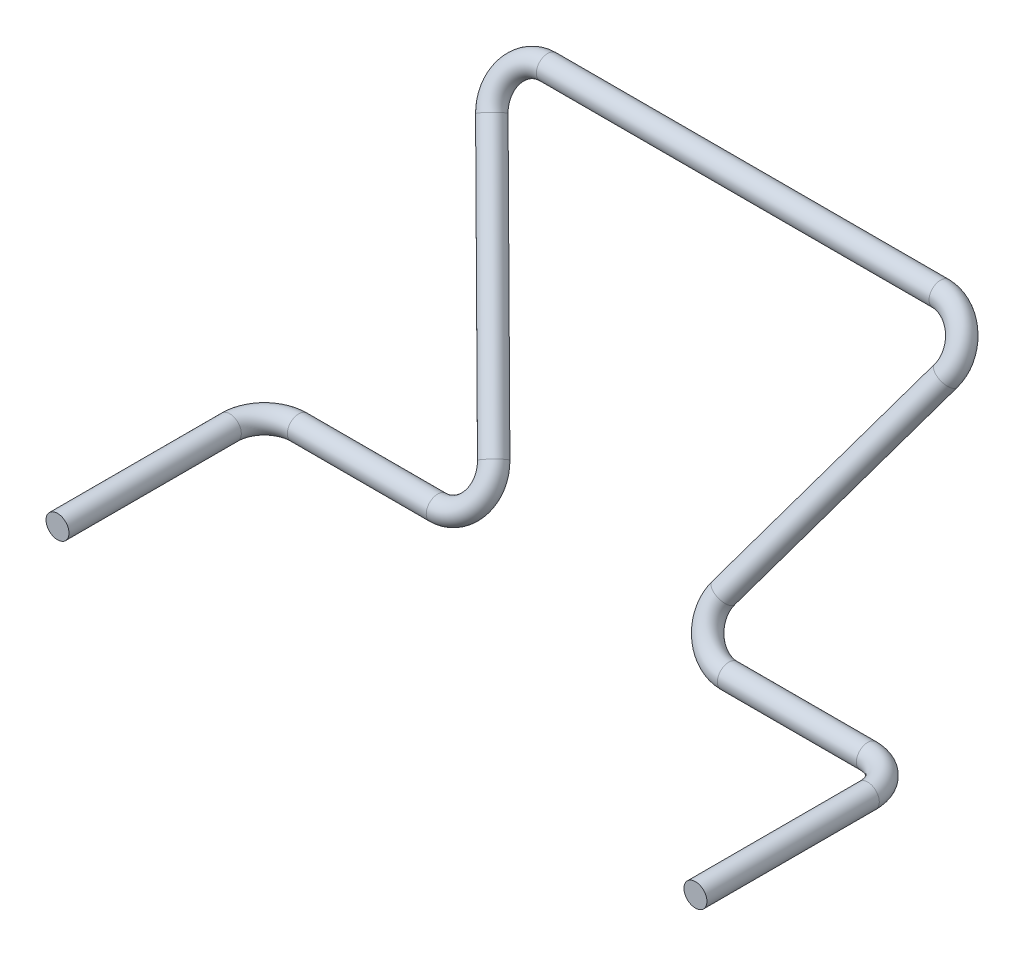
SolidWorks part; units mm, degrees
ref_plane "Front Plane" through (0, 0, 0) normal (0, 0, 1) x (1, 0, 0)
ref_plane "Top Plane" through (0, 0, 0) normal (0, 1, 0) x (1, 0, 0)
ref_plane "Right Plane" through (0, 0, 0) normal (1, 0, 0) x (0, 0, -1)
sketch3d "3DSketch2"
  line L0 (-27.7615, 0, 18) -> (-27.7615, 0, 3)
  line L1 (-24.7615, 0, 0) -> (-12.6698, 0, 0)
  line L2 (-10, 3.7731, -2.201) -> (-19.7615, 20.2269, -11.799)
  line L3 (-17.0917, 24, -14) -> (0, 24, -14)
  arc A0 (-19.7615, 20.2269, -11.799) -> (-17.0917, 24, -14) centre (-17.0917, 21.4087, -12.4884) ccw
  arc A1 (-12.6698, 0, 0) -> (-10, 3.7731, -2.201) centre (-12.6698, 2.5913, -1.5116) ccw
  arc A2 (-27.7615, 0, 3) -> (-24.7615, 0, 0) centre (-24.7615, 0, 3) ccw
  point P7 (-22, 24, -14)
  point P8 (-17.0917, 19.8971, -15.0797)
  point P11 (-7.7615, 0, 0)
  point P12 (-12.6698, 4.1029, 1.0797)
  point P15 (-27.7615, 0, 0)
  point P16 (-24.7615, -3, 3)
  point P17 (-5.8504, 0, 2.8877)
  point P18 (0, 0, 0)
  point P19 (0, 0, 0)
  point P20 (0.1262, 24, -14)
  point P21 (0, 0, 0)
  point P22 (-28.0539, 0, 22.7416)
  point P23 (-7.775, 0, 0.2142)
  point P24 (-24.7963, 0, 0.5516)
  point P25 (0, 0, 0)
  point P26 (0, 0, 0)
  point P27 (0, 0, 0)
  dimension "D1" = 3
  dimension "D2" = 18
  dimension "D3" = 20
  dimension "D4" = 22
  dimension "D5" = 10
  dimension "D7" = 24
  dimension "D6" = 14
  dimension "D8" = 18
sweep "Sweep2" add path "3DSketch2" circular profile diameter 2 parameters "D3"=2
mirror "Mirror1" about plane through (0, 0, 0) normal (1, 0, 0) of "Sweep2"
